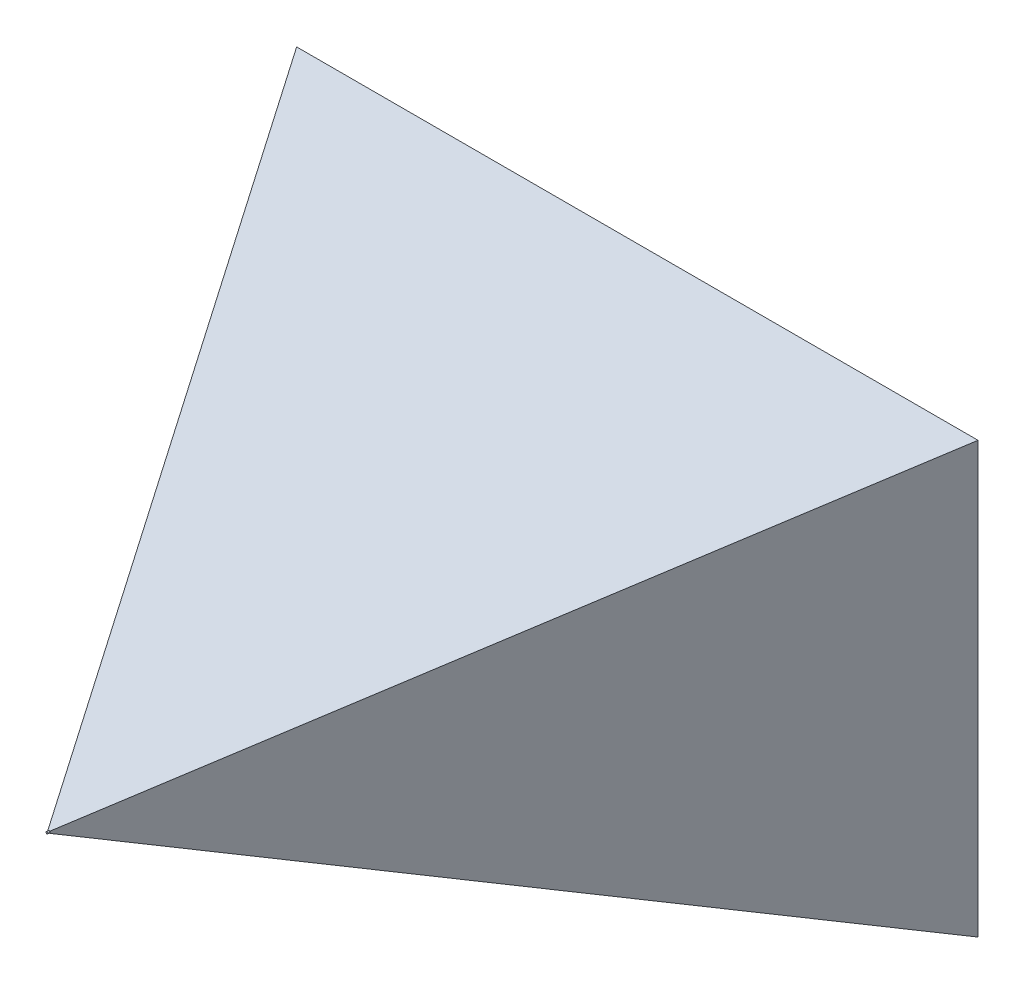
SolidWorks part; units mm, degrees
ref_plane "Front Plane" through (0, 0, 0) normal (0, 0, 1) x (1, 0, 0)
ref_plane "Top Plane" through (0, 0, 0) normal (0, 1, 0) x (1, 0, 0)
ref_plane "Right Plane" through (0, 0, 0) normal (1, 0, 0) x (0, 0, -1)
sketch "Sketch1" plane through (0, 0, 0) normal (0, 0, 1) x (1, 0, 0)
  line L1 (0, 0) -> (800, 0)
  line L2 (0, 0) -> (0, 800)
  line L3 (0, 800) -> (800, 800)
  line L4 (800, 0) -> (800, 800)
  dimension "D1" = 800
  dimension "D2" = 800
extrude "Boss-Extrude1" add sketch "Sketch1" along normal blind 600
sketch "Sketch2" plane through (800, 0, 0) normal (1, 0, 0) x (0, 0, -1)
  line L0 (-600, 800) -> (-600, 401)
  line L1 (-600, 0) -> (-600, 800) construction
  line L2 (-600, 401) -> (496.2435, 800)
  line L3 (-600, 800) -> (0, 800) construction
  line L4 (496.2435, 800) -> (-600, 800)
  line L6 (-600, 0) -> (0, 0) construction
  line L7 (496.2435, 0) -> (-600, 0)
  line L9 (-600, 0) -> (-600, 399)
  line L10 (-600, 399) -> (496.2435, 0)
  point P13 (0, 0)
  point P15 (-600, 420.0395)
  point P16 (-600, 400)
  dimension "D1" = 20
  dimension "D2" = 1
  dimension "D3" = 2
  dimension "D4" = 20
sketch "Sketch3" plane through (0, 0, 0) normal (0, -1, 0) x (1, 0, 0)
  line L0 (401, 600) -> (800, -91.0883)
  line L2 (800, -496.2435) -> (800, 600) construction
  line L3 (800, -91.0883) -> (800, 600)
  line L4 (800, 600) -> (401, 600)
  line L6 (0, 600) -> (0, -91.0883)
  line L7 (0, 600) -> (0, 0) construction
  line L9 (0, 600) -> (800, 600) construction
  line L10 (399, 600) -> (0, 600)
  line L11 (0, -91.0883) -> (399, 600)
  point P2 (402, 600)
  point P6 (402, 600)
  point P15 (0, 0)
  dimension "D1" = 2
  dimension "D2" = 30
  dimension "D3" = 401
  dimension "D4" = 30
sketch "Sketch4" plane through (0, 0, 600) normal (0, 0, 1) x (1, 0, 0)
  line L1 (0, 800) -> (800, 0) construction
  line L5 (800, 800) -> (0, 0) construction
  line L9 (800, 800) -> (800, 401) construction
  circle A0 centre (400, 400) radius 1
  point P4 (0, 0)
  point P7 (0, 0)
  point P8 (0, 0)
  point P9 (0, 0)
  point P10 (0, 0)
  point P11 (0, 0)
  point P12 (0, 0)
  point P13 (0, 0)
  point P14 (0, 129.4624)
  point P15 (0, 0)
  point P16 (0, 0)
  point P17 (400, 400)
  point P18 (400, 0)
  point P19 (0, 0)
  point P25 (0, 0)
  point P27 (800, 555.5324)
  point P30 (0, 365.3824)
  point P31 (0, 0)
  point P32 (0, 0)
  point P34 (0, 0)
  dimension "D1" = 2
extrude "Cut-Extrude1" cut sketch "Sketch2" against normal through all
extrude "Cut-Extrude2" cut sketch "Sketch3" against normal through all
extrude "Boss-Extrude2" add sketch "Sketch4" along normal blind 2
